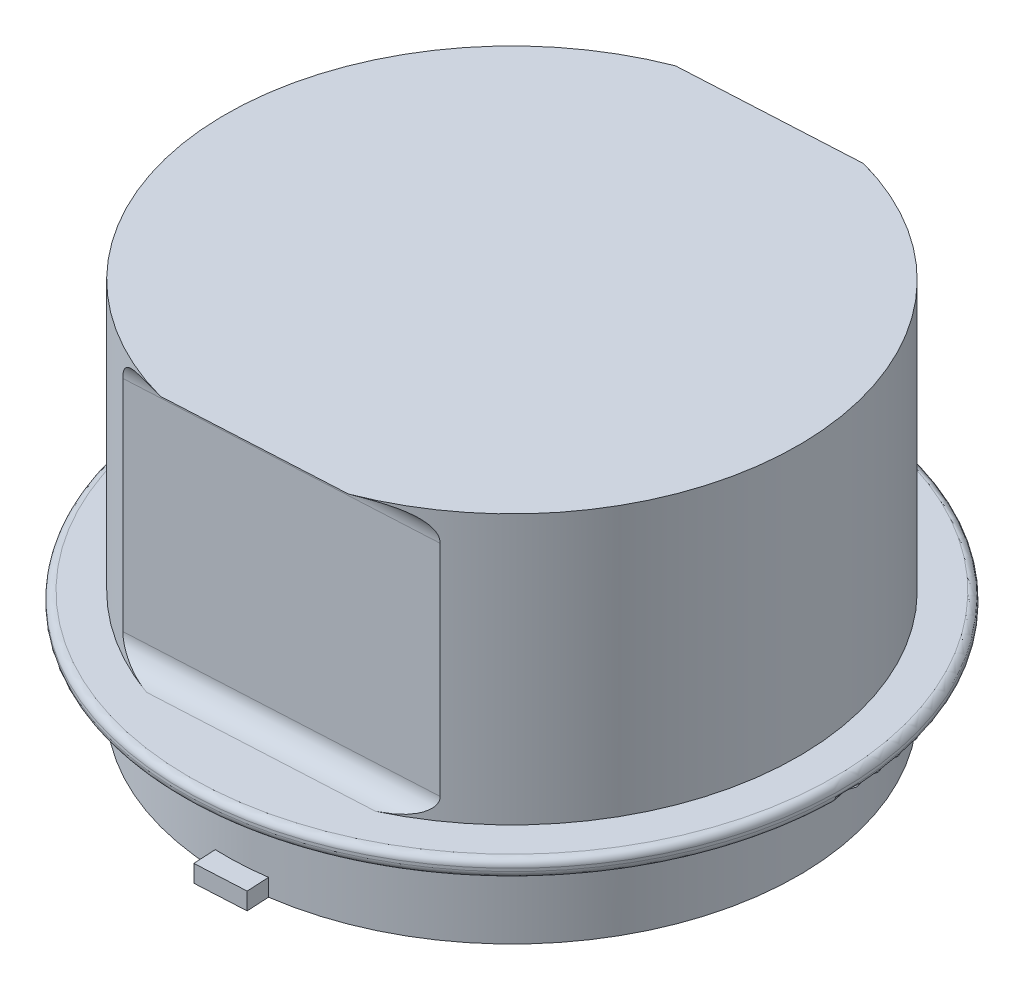
SolidWorks part; units mm, degrees
ref_plane "Front Plane" through (0, 0, 0) normal (0, 0, 1) x (1, 0, 0)
ref_plane "Top Plane" through (0, 0, 0) normal (0, 1, 0) x (1, 0, 0)
ref_plane "Right Plane" through (0, 0, 0) normal (1, 0, 0) x (0, 0, -1)
sketch "Sketch1" plane through (0, 0, 0) normal (0, 0, 1) x (1, 0, 0)
  line L0 (0, 25.4) -> (0, 1.524)
  line L1 (0, -7.62) -> (25.4, -7.62)
  line L2 (25.4, -7.62) -> (25.4, 25.4)
  line L3 (25.4, 25.4) -> (0, 25.4)
  line L4 (0, 0) -> (-3.175, 0)
  line L5 (-3.81, 0.635) -> (-3.81, 0.889)
  line L6 (-3.175, 1.524) -> (0, 1.524)
  line L7 (0, 0) -> (0, -7.62)
  arc A0 (-3.81, 0.889) -> (-3.175, 1.524) centre (-3.175, 0.889) cw
  arc A1 (-3.175, 0) -> (-3.81, 0.635) centre (-3.175, 0.635) cw
  point P12 (-3.81, 1.524)
  point P15 (-3.81, 0)
  dimension "D6" = 0.635
  dimension "D7" = 0.635
  dimension "D1" = 33.02
  dimension "D2" = 25.4
  dimension "D3" = 7.62
  dimension "D4" = 1.524
  dimension "D5" = 3.81
revolve "Revolve2" add sketch "Sketch1" angle 360 about L2
sketch "Sketch3" plane through (0, -7.62, 0) normal (0, -1, 0) x (1, 0, 0)
  circle A0 centre (25.4, 0) radius 25.4 construction
  point P0 (0.0352, 1.3359)
ref_plane "Plane1" through (0.0352, -7.62, 1.3359) normal (-0.9986, 0, 0.0526) x (0.0526, 0, 0.9986)
sketch "Sketch4" plane through (0.0352, -7.62, 1.3359) normal (-0.9986, 0, 0.0526) x (0.0526, 0, 0.9986)
  line L0 (-23.495, 9.144) -> (-26.67, 9.144)
  line L1 (0, 0) -> (-21.59, 0)
  line L2 (0, 0) -> (0, 9.144)
  line L3 (0, 9.144) -> (-21.59, 9.144)
  line L4 (-21.59, 0) -> (-21.59, 9.144)
  line L5 (-26.67, 9.144) -> (-26.67, 33.02)
  line L6 (-26.67, 33.02) -> (-24.13, 33.02)
  line L7 (-21.59, 30.48) -> (-21.59, 11.049)
  line L8 (0, 9.144) -> (0, 33.02) construction
  line L9 (21.59, 30.48) -> (21.59, 11.049)
  line L10 (23.495, 9.144) -> (26.67, 9.144)
  line L11 (26.67, 9.144) -> (26.67, 33.02)
  line L12 (26.67, 33.02) -> (24.13, 33.02)
  arc A0 (-21.59, 30.48) -> (-24.13, 33.02) centre (-24.13, 30.48) ccw
  arc A1 (-23.495, 9.144) -> (-21.59, 11.049) centre (-23.495, 11.049) ccw
  arc A2 (23.495, 9.144) -> (21.59, 11.049) centre (23.495, 11.049) cw
  arc A3 (21.59, 30.48) -> (24.13, 33.02) centre (24.13, 30.48) cw
  point P10 (-21.59, 33.02)
  dimension "D5" = 2.54
  dimension "D6" = 1.905
  dimension "D1" = 9.144
  dimension "D2" = 21.59
  dimension "D3" = 5.08
  dimension "D4" = 23.876
extrude "Cut-Extrude1" cut sketch "Sketch4" against normal blind 57.404 contours L7 A1 L0 L5 L6 A0 | L9 A2 L10 L11 L12 A3
ref_plane "Plane2" through (26.7359, 0, 25.3648) normal (0.0526, 0, 0.9986) x (0.9986, 0, -0.0526)
sketch "Sketch5" plane through (26.7359, 0, 25.3648) normal (0.0526, 0, 0.9986) x (0.9986, 0, -0.0526)
  line L1 (-2.2479, -6.096) -> (2.2479, -6.096)
  line L2 (-2.2479, -6.096) -> (-2.2479, -7.62)
  line L3 (-2.2479, -7.62) -> (2.2479, -7.62)
  line L4 (2.2479, -6.096) -> (2.2479, -7.62)
  line L5 (13.3803, 3.429) -> (-13.3803, 3.429) construction
  line L7 (0, 3.429) -> (0, -7.62) construction
  point P8 (0, 3.429)
  point P9 (0, -7.62)
  dimension "D1" = 4.4958
  dimension "D2" = 1.524
extrude "Boss-Extrude1" add sketch "Sketch5" along normal blind 1.905 and the other way blind 52.705
